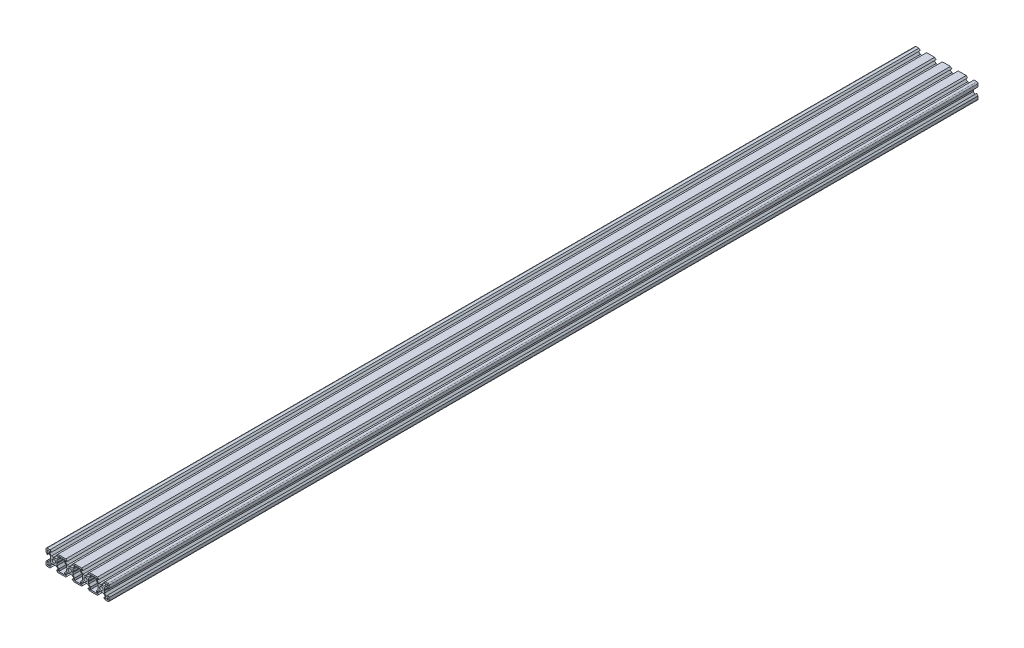
SolidWorks part; units mm, degrees
ref_plane "Front Plane" through (0, 0, 0) normal (0, 0, 1) x (1, 0, 0)
ref_plane "Top Plane" through (0, 0, 0) normal (0, 1, 0) x (1, 0, 0)
ref_plane "Right Plane" through (0, 0, 0) normal (1, 0, 0) x (0, 0, -1)
sketch "Sketch1" plane through (0, 0, 0) normal (0, 0, 1) x (1, 0, 0)
  line L0 (4.9, -10) -> (15.0977, -10)
  line L1 (-8.2011, 3.1) -> (-10.0011, 4.9)
  line L2 (-3.1, 8.2) -> (-5.4, 8.2)
  line L3 (-5.4, 8.2) -> (-5.4, 6.3)
  line L4 (-5.4, 6.3) -> (-3.1, 4)
  line L5 (-3.1, 4) -> (-0.5, 4)
  line L6 (3.1, 4) -> (5.4, 6.3)
  line L7 (5.4, 6.3) -> (5.4, 8.2)
  line L8 (5.4, 8.2) -> (3.1, 8.2)
  line L9 (-8.2135, -3.1) -> (-10.0011, -4.8876)
  line L10 (4.9, 10) -> (15.0977, 10)
  line L11 (0.5, 4) -> (3.1, 4)
  line L12 (5.4, -8.2) -> (3.1, -8.2)
  line L13 (5.4, -6.3) -> (5.4, -8.2)
  line L14 (3.1, -4) -> (5.4, -6.3)
  line L15 (-3.1, -4) -> (-0.5, -4)
  line L16 (-5.4, -6.3) -> (-3.1, -4)
  line L17 (-5.4, -8.2) -> (-5.4, -6.3)
  line L18 (-3.1, -8.2) -> (-5.4, -8.2)
  line L19 (-4.0135, 0.5) -> (-4.0135, 3.1)
  line L20 (-10.0011, -4.8876) -> (-10.0011, -8.5)
  line L21 (0.5, -4) -> (3.1, -4)
  line L22 (-8.2135, -3.1) -> (-8.2135, -5.4)
  line L23 (-8.2135, -5.4) -> (-6.3135, -5.4)
  line L24 (-6.3135, -5.4) -> (-4.0135, -3.1)
  line L25 (-4.0135, -3.1) -> (-4.0135, -0.5)
  line L26 (-4.0135, 3.1) -> (-6.3135, 5.4)
  line L27 (-6.3135, 5.4) -> (-8.2135, 5.4)
  line L28 (-8.2135, 5.4) -> (-8.2011, 3.1)
  line L29 (3.9989, 0.5) -> (3.9989, 3.1)
  line L30 (6.2989, 5.4) -> (6.2989, 8.2)
  line L31 (6.2989, -5.4) -> (6.2989, -8.2)
  line L32 (6.2989, -8.2) -> (13.6989, -8.2)
  line L33 (3.9989, 3.1) -> (6.2989, 5.4)
  line L34 (3.9989, -3.1) -> (3.9989, -0.5)
  line L35 (6.2989, -5.4) -> (3.9989, -3.1)
  line L36 (13.6989, -5.4) -> (13.6989, -8.2)
  line L37 (24.8977, 10) -> (35.1, 10)
  line L38 (24.8977, -10) -> (35.1, -10)
  line L39 (26.3113, -5.4) -> (26.3113, -8.2)
  line L40 (-10.0011, 8.5) -> (-10.0011, 4.9)
  line L41 (-8.5011, 10) -> (-4.9, 10)
  line L42 (-10.0011, 8.5) -> (-10.0011, 4.9)
  line L43 (-8.5011, -10) -> (-4.9, -10)
  line L44 (6.2989, 8.2) -> (13.6989, 8.2)
  line L45 (-8.2011, 7.0732) -> (-8.2011, 7.7)
  line L46 (-7.7011, 8.2) -> (-7.0738, 8.2)
  line L47 (-6.8971, 7.7732) -> (-7.7744, 6.8964)
  line L48 (-3.1, 8.2) -> (-4.9, 10)
  line L49 (3.1, 8.2) -> (4.9, 10)
  line L50 (-3.1, -8.2) -> (-4.9, -10)
  line L51 (3.1, -8.2) -> (4.9, -10)
  line L52 (36.9, 8.2) -> (34.6, 8.2)
  line L53 (34.6, 8.2) -> (34.6, 6.3)
  line L54 (13.6989, 8.2) -> (13.6989, 5.4)
  line L55 (34.6, 6.3) -> (36.9, 4)
  line L56 (36.9, 4) -> (39.5, 4)
  line L57 (43.1, 4) -> (45.4, 6.3)
  line L58 (45.4, 6.3) -> (45.4, 8.2)
  line L59 (45.4, 8.2) -> (43.1, 8.2)
  line L60 (-6.8971, -7.7732) -> (-7.7744, -6.8964)
  line L61 (-7.7011, -8.2) -> (-7.0738, -8.2)
  line L62 (-8.2011, -7.0732) -> (-8.2011, -7.7)
  line L63 (26.3113, -8.2) -> (33.6865, -8.2)
  line L64 (33.6865, -8.2) -> (33.6865, -5.4)
  line L65 (26.3113, 5.4) -> (26.3113, 8.2)
  line L66 (40.5, 4) -> (43.1, 4)
  line L67 (45.4, -8.2) -> (43.1, -8.2)
  line L68 (45.4, -6.3) -> (45.4, -8.2)
  line L69 (43.1, -4) -> (45.4, -6.3)
  line L70 (36.9, -4) -> (39.5, -4)
  line L71 (34.6, -6.3) -> (36.9, -4)
  line L72 (34.6, -8.2) -> (34.6, -6.3)
  line L73 (16.8977, -8.2) -> (15.0977, -10)
  line L74 (23.0977, -8.2) -> (24.8977, -10)
  line L75 (16.8977, 8.2) -> (15.0977, 10)
  line L76 (23.0977, 8.2) -> (24.8977, 10)
  line L77 (26.3113, 8.2) -> (33.6865, 8.2)
  line L78 (33.6865, 8.2) -> (33.6865, 5.4)
  line L84 (36.9, -8.2) -> (34.6, -8.2)
  line L85 (35.9865, 0.5) -> (35.9865, 3.1)
  line L86 (40.5, -4) -> (43.1, -4)
  line L87 (13.6989, -5.4) -> (15.9989, -3.1)
  line L88 (15.9989, -3.1) -> (15.9989, -0.5)
  line L89 (15.9989, 3.1) -> (13.6989, 5.4)
  line L92 (15.9989, 0.5) -> (15.9989, 3.1)
  line L95 (24.0113, 3.1) -> (26.3113, 5.4)
  line L96 (24.0113, -3.1) -> (24.0113, -0.5)
  line L97 (26.3113, -5.4) -> (24.0113, -3.1)
  line L100 (19.4977, -4) -> (16.8977, -4)
  line L102 (24.0113, 0.5) -> (24.0113, 3.1)
  line L103 (23.0977, -8.2) -> (25.3977, -8.2)
  line L104 (25.3977, -8.2) -> (25.3977, -6.3)
  line L105 (25.3977, -6.3) -> (23.0977, -4)
  line L106 (23.0977, -4) -> (20.4977, -4)
  line L107 (16.8977, -4) -> (14.5977, -6.3)
  line L108 (14.5977, -6.3) -> (14.5977, -8.2)
  line L109 (14.5977, -8.2) -> (16.8977, -8.2)
  line L110 (19.4977, 4) -> (16.8977, 4)
  line L111 (33.6865, -5.4) -> (35.9865, -3.1)
  line L113 (14.5977, 8.2) -> (16.8977, 8.2)
  line L114 (14.5977, 6.3) -> (14.5977, 8.2)
  line L115 (16.8977, 4) -> (14.5977, 6.3)
  line L116 (23.0977, 4) -> (20.4977, 4)
  line L117 (25.3977, 6.3) -> (23.0977, 4)
  line L118 (25.3977, 8.2) -> (25.3977, 6.3)
  line L119 (23.0977, 8.2) -> (25.3977, 8.2)
  line L121 (35.9865, -3.1) -> (35.9865, -0.5)
  line L122 (35.9865, 3.1) -> (33.6865, 5.4)
  line L125 (43.9989, 0.5) -> (43.9989, 3.1)
  line L126 (43.9989, 3.1) -> (46.2989, 5.4)
  line L127 (43.9989, -3.1) -> (43.9989, -0.5)
  line L128 (46.2989, -5.4) -> (43.9989, -3.1)
  line L134 (36.9, 8.2) -> (35.1, 10)
  line L135 (43.1, 8.2) -> (44.9, 10)
  line L136 (36.9, -8.2) -> (35.1, -10)
  line L137 (43.1, -8.2) -> (44.9, -10)
  line L140 (68.1989, -7.0732) -> (68.1989, -7.7)
  line L141 (67.6989, -8.2) -> (67.0716, -8.2)
  line L142 (66.8948, -7.7732) -> (67.7721, -6.8964)
  line L143 (46.2989, 8.2) -> (46.2989, 5.4)
  line L144 (56.8977, -8.2) -> (55.0977, -10)
  line L145 (63.0977, -8.2) -> (64.8977, -10)
  line L146 (56.8977, 8.2) -> (55.0977, 10)
  line L147 (63.0977, 8.2) -> (64.8977, 10)
  line L148 (66.8948, 7.7732) -> (67.7721, 6.8964)
  line L149 (67.6989, 8.2) -> (67.0716, 8.2)
  line L150 (68.1989, 7.0732) -> (68.1989, 7.7)
  line L151 (53.6989, 8.2) -> (46.2989, 8.2)
  line L152 (68.4989, -10) -> (64.8977, -10)
  line L153 (69.9989, 8.5) -> (69.9989, 4.9)
  line L154 (68.4989, 10) -> (64.8977, 10)
  line L155 (69.9989, 8.5) -> (69.9989, 4.9)
  line L157 (46.2989, -5.4) -> (46.2989, -8.2)
  line L158 (53.6989, -5.4) -> (55.9989, -3.1)
  line L159 (55.9989, -3.1) -> (55.9989, -0.5)
  line L160 (55.9989, 3.1) -> (53.6989, 5.4)
  line L161 (53.6989, -8.2) -> (46.2989, -8.2)
  line L162 (53.6989, -5.4) -> (53.6989, -8.2)
  line L163 (53.6989, 5.4) -> (53.6989, 8.2)
  line L164 (55.9989, 0.5) -> (55.9989, 3.1)
  line L165 (68.2113, 5.4) -> (68.1989, 3.1)
  line L166 (66.3113, 5.4) -> (68.2113, 5.4)
  line L167 (64.0113, 3.1) -> (66.3113, 5.4)
  line L168 (64.0113, -3.1) -> (64.0113, -0.5)
  line L169 (66.3113, -5.4) -> (64.0113, -3.1)
  line L170 (68.2113, -5.4) -> (66.3113, -5.4)
  line L171 (68.2113, -3.1) -> (68.2113, -5.4)
  line L172 (59.4977, -4) -> (56.8977, -4)
  line L173 (69.9989, -4.8876) -> (69.9989, -8.5)
  line L174 (64.0113, 0.5) -> (64.0113, 3.1)
  line L175 (63.0977, -8.2) -> (65.3977, -8.2)
  line L176 (65.3977, -8.2) -> (65.3977, -6.3)
  line L177 (65.3977, -6.3) -> (63.0977, -4)
  line L178 (63.0977, -4) -> (60.4977, -4)
  line L179 (56.8977, -4) -> (54.5977, -6.3)
  line L180 (54.5977, -6.3) -> (54.5977, -8.2)
  line L181 (54.5977, -8.2) -> (56.8977, -8.2)
  line L182 (59.4977, 4) -> (56.8977, 4)
  line L183 (55.0977, 10) -> (44.9, 10)
  line L184 (68.2113, -3.1) -> (69.9989, -4.8876)
  line L185 (54.5977, 8.2) -> (56.8977, 8.2)
  line L186 (54.5977, 6.3) -> (54.5977, 8.2)
  line L187 (56.8977, 4) -> (54.5977, 6.3)
  line L188 (63.0977, 4) -> (60.4977, 4)
  line L189 (65.3977, 6.3) -> (63.0977, 4)
  line L190 (65.3977, 8.2) -> (65.3977, 6.3)
  line L191 (63.0977, 8.2) -> (65.3977, 8.2)
  line L192 (68.1989, 3.1) -> (69.9989, 4.9)
  line L193 (55.0977, -10) -> (44.9, -10)
  circle A0 centre (0, 0) radius 2.1
  arc A1 (-10.0011, -8.5) -> (-8.5011, -10) centre (-8.5011, -8.5) ccw
  arc A2 (0.5, -4) -> (-0.5, -4) centre (0, -4) ccw
  arc A3 (20.4977, -4) -> (19.4977, -4) centre (19.9977, -4) ccw
  arc A4 (-8.5011, 10) -> (-10.0011, 8.5) centre (-8.5011, 8.5) ccw
  arc A5 (-8.2011, 7.7) -> (-7.7011, 8.2) centre (-7.7011, 7.7) cw
  arc A6 (-7.0738, 8.2) -> (-6.8971, 7.7732) centre (-7.0738, 7.95) cw
  arc A7 (-8.2011, 7.0732) -> (-7.7744, 6.8964) centre (-7.9511, 7.0732) ccw
  arc A8 (-0.5, 4) -> (0.5, 4) centre (0, 4) ccw
  circle A9 centre (40, 0) radius 2.1
  arc A10 (-4.0135, -0.5) -> (-4.0135, 0.5) centre (-4.0135, 0) ccw
  arc A11 (3.9989, 0.5) -> (3.9989, -0.5) centre (3.9989, 0) ccw
  arc A17 (39.5, 4) -> (40.5, 4) centre (40, 4) ccw
  arc A18 (-8.2011, -7.0732) -> (-7.7744, -6.8964) centre (-7.9511, -7.0732) cw
  arc A19 (-7.0738, -8.2) -> (-6.8971, -7.7732) centre (-7.0738, -7.95) ccw
  arc A20 (-8.2011, -7.7) -> (-7.7011, -8.2) centre (-7.7011, -7.7) ccw
  arc A24 (35.9865, -0.5) -> (35.9865, 0.5) centre (35.9865, 0) ccw
  arc A25 (43.9989, 0.5) -> (43.9989, -0.5) centre (43.9989, 0) ccw
  arc A29 (68.1989, -7.7) -> (67.6989, -8.2) centre (67.6989, -7.7) cw
  arc A30 (15.9989, 0.5) -> (15.9989, -0.5) centre (15.9989, 0) cw
  arc A31 (24.0113, -0.5) -> (24.0113, 0.5) centre (24.0113, 0) cw
  arc A32 (67.0716, -8.2) -> (66.8948, -7.7732) centre (67.0716, -7.95) cw
  arc A33 (20.4977, 4) -> (19.4977, 4) centre (19.9977, 4) cw
  arc A38 (68.1989, -7.0732) -> (67.7721, -6.8964) centre (67.9489, -7.0732) ccw
  arc A39 (55.9989, 0.5) -> (55.9989, -0.5) centre (55.9989, 0) cw
  circle A41 centre (19.9977, 0) radius 2.1
  arc A42 (64.0113, -0.5) -> (64.0113, 0.5) centre (64.0113, 0) cw
  arc A43 (60.4977, 4) -> (59.4977, 4) centre (59.9977, 4) cw
  arc A44 (68.1989, 7.0732) -> (67.7721, 6.8964) centre (67.9489, 7.0732) cw
  arc A45 (67.0716, 8.2) -> (66.8948, 7.7732) centre (67.0716, 7.95) ccw
  arc A46 (68.1989, 7.7) -> (67.6989, 8.2) centre (67.6989, 7.7) ccw
  arc A47 (68.4989, 10) -> (69.9989, 8.5) centre (68.4989, 8.5) cw
  arc A48 (39.5, -4) -> (40.5, -4) centre (40, -4) cw
  arc A49 (59.4977, -4) -> (60.4977, -4) centre (59.9977, -4) cw
  arc A50 (69.9989, -8.5) -> (68.4989, -10) centre (68.4989, -8.5) cw
  circle A51 centre (59.9977, 0) radius 2.1
extrude "Boss-Extrude1" add sketch "Sketch1" along normal blind 1100 contours A50 L173 L184 L171 L170 L169 L168 A42 L174 L167 L166 L165 L192 L153 A47 L154 L147 L191 L190 L189 L188 A43 L182 L187 L186 L185 L146 L183 L135 L59 L58 L57 L66 A17 L56 L55 L53 L52 L134 L37 L76 L119 L118 L117 L116 A33 L110 L115 L114 L113 L75
ref_plane "Plane1" through (-10, 0, 0) normal (1, 0, 0) x (0, 0, -1)
